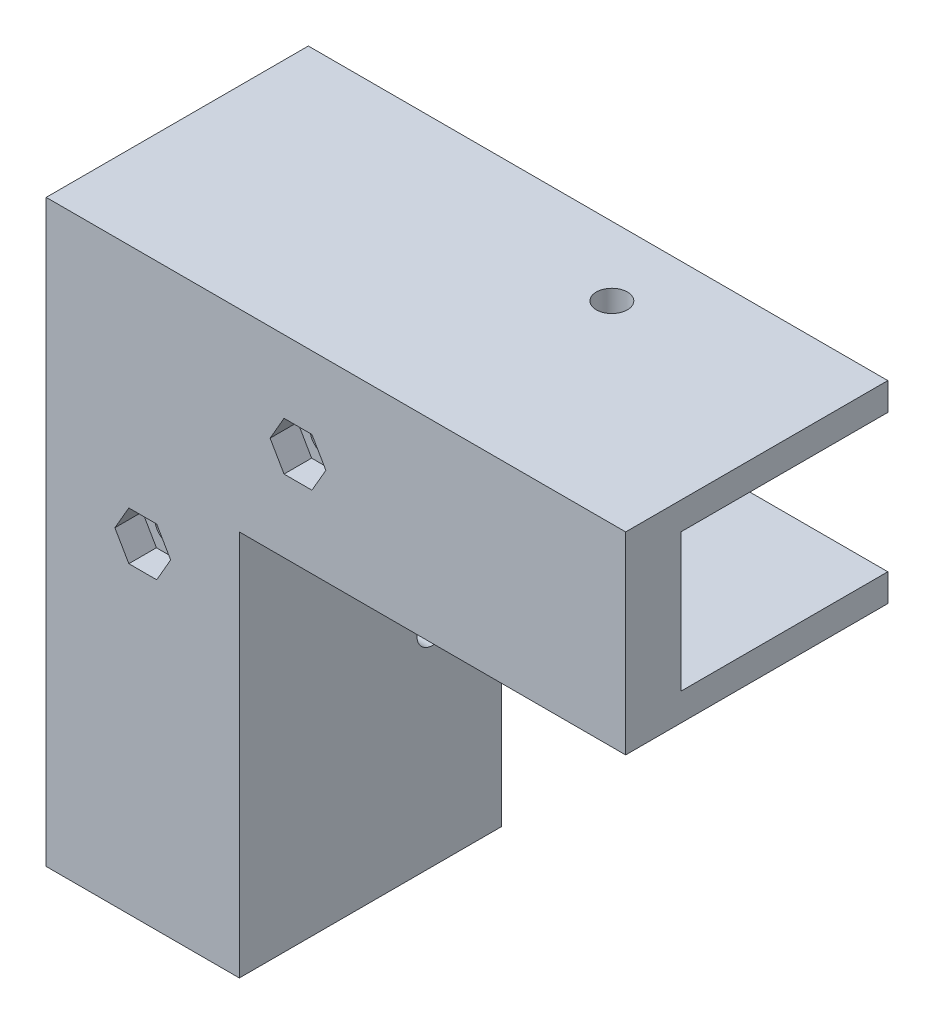
SolidWorks part; units mm, degrees
ref_plane "Plan de face" through (0, 0, 0) normal (0, 0, 1) x (1, 0, 0)
ref_plane "Plan de dessus" through (0, 0, 0) normal (0, 1, 0) x (1, 0, 0)
ref_plane "Plan de droite" through (0, 0, 0) normal (1, 0, 0) x (0, 0, -1)
sketch "Esquisse1" plane through (0, 0, 0) normal (0, 0, 1) x (1, 0, 0)
  line L0 (0, 0) -> (0, 60)
  line L1 (0, 60) -> (60, 60)
  line L2 (60, 60) -> (60, 80)
  line L3 (60, 80) -> (-20, 80)
  line L4 (-20, 80) -> (-20, 0)
  line L5 (-20, 0) -> (0, 0)
  dimension "D1" = 60
  dimension "D2" = 60
  dimension "D3" = 20
  dimension "D4" = 20
extrude "Boss.-Extru.1" add sketch "Esquisse1" along normal blind 8
sketch "Esquisse2" plane through (0, 0, 8) normal (0, 0, 1) x (1, 0, 0)
  line L0 (-12.0207, 51) -> (-7.9793, 44) construction
  line L1 (-20, 80) -> (-20, 0) construction
  line L3 (-5.9585, 47.5) -> (-14.0415, 47.5) construction
  line L5 (60, 80) -> (-20, 80) construction
  line L6 (0, 0) -> (0, 60) construction
  line L7 (-14.0415, 47.5) -> (-12.0207, 51)
  line L8 (-12.0207, 51) -> (-7.9793, 51)
  line L9 (-7.9793, 51) -> (-5.9585, 47.5)
  line L10 (-5.9585, 47.5) -> (-7.9793, 44)
  line L11 (-7.9793, 44) -> (-12.0207, 44)
  line L12 (-12.0207, 44) -> (-14.0415, 47.5)
  line L13 (10.4793, 66.5) -> (14.5207, 73.5) construction
  line L14 (16.5415, 70) -> (8.4585, 70) construction
  line L15 (-5.9585, 47.5) -> (-6.29, 47.0056)
  line L20 (-12.0207, 44) -> (-12.0207, 51) construction
  line L23 (8.4585, 70) -> (10.4793, 73.5)
  line L24 (10.4793, 73.5) -> (14.5207, 73.5)
  line L25 (14.5207, 73.5) -> (16.5415, 70)
  line L26 (16.5415, 70) -> (14.5207, 66.5)
  line L27 (14.5207, 66.5) -> (10.4793, 66.5)
  line L28 (10.4793, 66.5) -> (8.4585, 70)
  line L31 (16.5415, 70) -> (16.21, 69.5056)
  line L36 (10.4793, 66.5) -> (10.4793, 73.5) construction
  point P26 (-10, 47.5)
  point P27 (12.5, 70)
  dimension "D2" = 32.5
  dimension "D3" = 7
  dimension "D4" = 7
  dimension "D6" = 120
  dimension "D7" = 30
  dimension "D8" = 7
  dimension "D9" = 7
  dimension "D10" = 7
  dimension "D11" = 120
  dimension "D12" = 30
  dimension "D13" = 10
  dimension "D14" = 10
  dimension "D15" = 32.5
extrude "Enlèv. mat.-Extru.1" cut sketch "Esquisse2" against normal blind 4
sketch "Esquisse3" plane through (0, 0, 4) normal (0, 0, 1) x (1, 0, 0)
  line L0 (-7.9793, 51) -> (-5.9585, 47.5) construction
  line L1 (-14.0415, 47.5) -> (-12.0207, 51) construction
  line L3 (10.4793, 73.5) -> (14.5207, 73.5) construction
  line L4 (16.5415, 70) -> (14.5207, 66.5) construction
  circle A0 centre (-10, 47.5) radius 2.25
  circle A1 centre (12.5, 70) radius 2.25
  dimension "D1" = 3.5
  dimension "D2" = 3.5
  dimension "D3" = 4.5
  dimension "D4" = 4.5
  dimension "D5" = 3.5
  dimension "D6" = 3.5
extrude "Enlèv. mat.-Extru.2" cut sketch "Esquisse3" against normal through all
sketch "Esquisse4" plane through (0, 0, 8) normal (0, 0, 1) x (1, 0, 0)
  line L0 (0, 0) -> (0, 60)
  line L2 (0, 60) -> (60, 60)
  line L3 (60, 60) -> (60, 56)
  line L4 (60, 56) -> (4, 56)
  line L5 (4, 56) -> (4, 0)
  line L6 (4, 0) -> (0, 0)
  line L7 (60, 80) -> (60, 84)
  line L8 (60, 84) -> (-24, 84)
  line L9 (-24, 84) -> (-24, 0)
  line L10 (-24, 0) -> (-20, 0)
  line L11 (-20, 0) -> (-20, 80)
  line L12 (-20, 80) -> (60, 80)
  dimension "D1" = 4
  dimension "D2" = 4
  dimension "D3" = 4
  dimension "D4" = 4
extrude "Boss.-Extru.2" add sketch "Esquisse4" against normal blind 38
sketch "Esquisse5" plane through (0, 56, 0) normal (0, -1, 0) x (1, 0, 0)
  line L0 (4, -30) -> (60, -30) construction
  line L1 (60, -30) -> (60, 8) construction
  circle A0 centre (30, -20) radius 2.25
  dimension "D1" = 4.5
  dimension "D2" = 10
  dimension "D3" = 30
extrude "Enlèv. mat.-Extru.3" cut sketch "Esquisse5" against normal through all
sketch "Esquisse6" plane through (4, 0, 0) normal (1, 0, 0) x (0, 0, -1)
  line L0 (30, 0) -> (30, 56) construction
  line L1 (30, 0) -> (-8, 0) construction
  circle A0 centre (20, 30) radius 2.25
  dimension "D1" = 4.5
  dimension "D2" = 10
  dimension "D3" = 30
extrude "Enlèv. mat.-Extru.4" cut sketch "Esquisse6" against normal through all
fillet "Congé1" radius 6 1 edges at (0, 60, -15)
